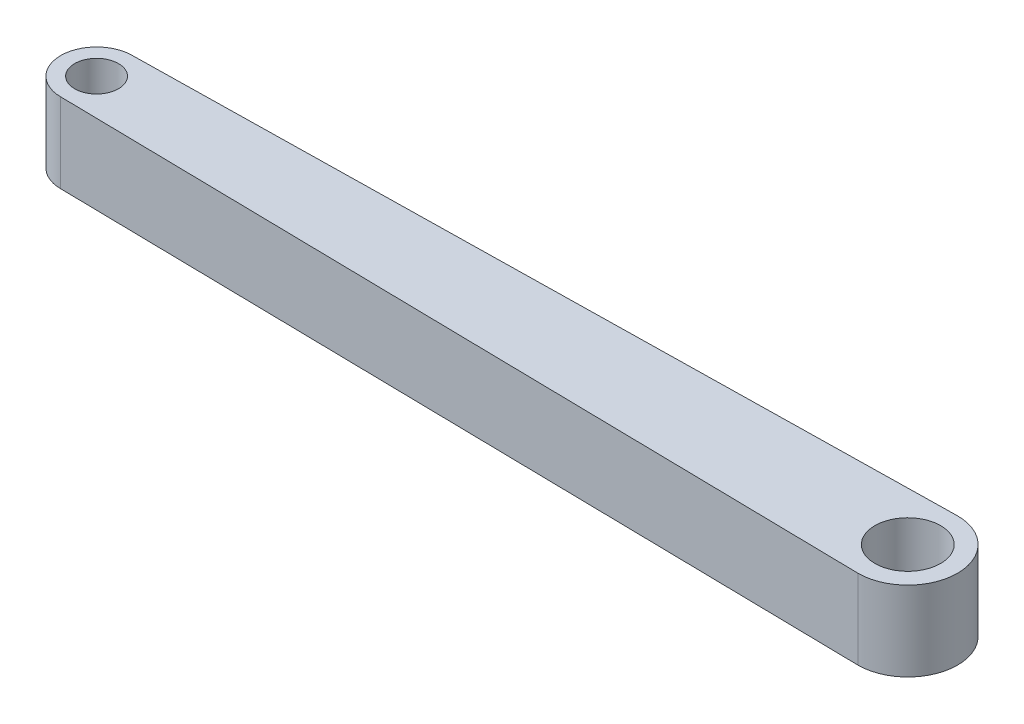
SolidWorks part; units mm, degrees
ref_plane "Front Plane" through (0, 0, 0) normal (0, 0, 1) x (1, 0, 0)
ref_plane "Top Plane" through (0, 0, 0) normal (0, 1, 0) x (1, 0, 0)
ref_plane "Right Plane" through (0, 0, 0) normal (1, 0, 0) x (0, 0, -1)
sketch "Sketch1" plane through (0, 0, 0) normal (0, 1, 0) x (1, 0, 0)
  line L0 (-10.19, 0) -> (10.19, 0) construction
  line L1 (-10.19, 0.9) -> (10.19, 1.25)
  line L2 (-10.19, -0.9) -> (10.19, -1.25)
  arc A0 (-10.19, 0.9) -> (-10.19, -0.9) centre (-10.19, 0) ccw
  circle A1 centre (-10.19, 0) radius 0.55
  circle A2 centre (10.19, 0) radius 0.825
  arc A3 (10.1471, -1.2493) -> (10.1471, 1.2493) centre (10.19, 0) ccw
  point P4 (0, 0)
  dimension "D1" = 1.1
  dimension "D2" = 1.8
  dimension "D3" = 1.65
  dimension "D4" = 2.5
  dimension "D5" = 20.38
extrude "Boss-Extrude1" add sketch "Sketch1" along normal blind 2
